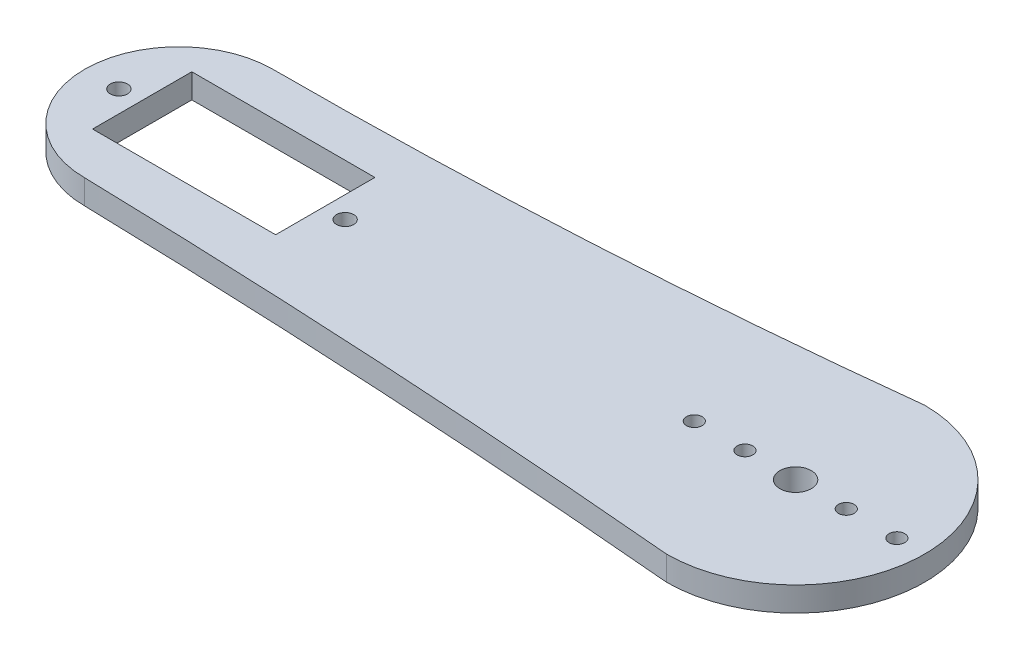
SolidWorks part; units mm, degrees
ref_plane "Front Plane" through (0, 0, 0) normal (0, 0, 1) x (1, 0, 0)
ref_plane "Top Plane" through (0, 0, 0) normal (0, 1, 0) x (1, 0, 0)
ref_plane "Right Plane" through (0, 0, 0) normal (1, 0, 0) x (0, 0, -1)
sketch "Sketch1" plane through (0, 0, 0) normal (0, 1, 0) x (1, 0, 0)
  line L0 (-71.588, 21.1358) -> (-71.588, 8.9358)
  line L2 (-71.588, 21.1358) -> (-49.088, 21.1358)
  line L3 (-49.088, 21.1358) -> (-49.088, 8.9358)
  line L4 (-49.088, 8.9358) -> (-71.588, 8.9358)
  arc A0 (-66.8835, 26.3799) -> (-66.8835, 3.2662) centre (-66.8835, 14.823) ccw
  arc A1 (8.9304, -1.0335) -> (8.9304, 30.6795) centre (8.9304, 14.823) ccw
  arc A2 (8.9304, -1.0335) -> (-66.8835, 3.2662) centre (-95.9348, -1179.5283) ccw
  circle A4 centre (-66.8835, 14.823) radius 2.1715
  circle A5 centre (8.9304, 14.823) radius 1.9302
  circle A6 centre (-74.238, 14.823) radius 1.0616
  circle A7 centre (-46.438, 14.823) radius 1.0616
  circle A8 centre (2.7054, 14.823) radius 0.9651
  circle A9 centre (-3.5196, 14.823) radius 0.9651
  circle A10 centre (15.1554, 14.823) radius 0.9651
  circle A11 centre (21.3804, 14.823) radius 0.9651
  arc A12 (-66.8835, 26.3799) -> (8.9304, 30.6795) centre (-66.8835, 696.9266) ccw
  point P0 (-71.588, 15.0358)
  point P25 (-78.4404, 14.823)
  dimension "D7" = 75.814
  dimension "D8" = 4.2023
  dimension "D5" = 2.65
  dimension "D6" = 2.65
extrude "Boss-Extrude1" add sketch "Sketch1" along normal blind 3
